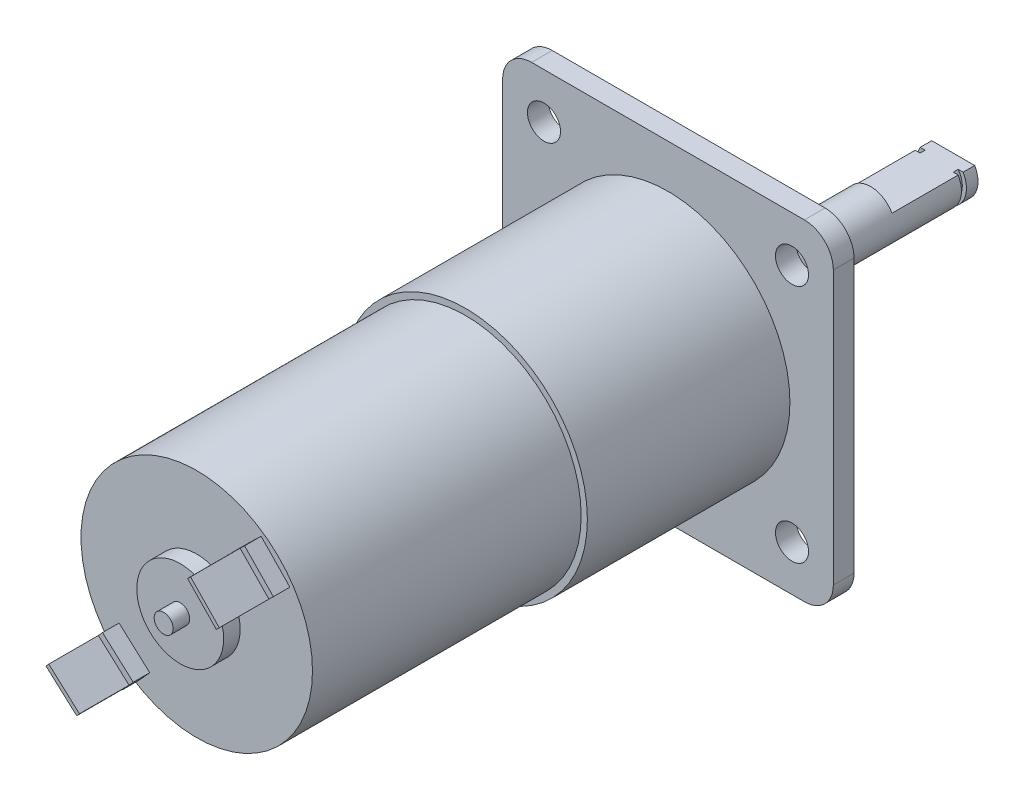
SolidWorks part; units mm, degrees
ref_plane "Alzado" through (0, 0, 0) normal (0, 0, 1) x (1, 0, 0)
ref_plane "Planta" through (0, 0, 0) normal (0, 1, 0) x (1, 0, 0)
ref_plane "Vista lateral" through (0, 0, 0) normal (1, 0, 0) x (0, 0, -1)
sketch "Croquis1" plane through (0, 0, 0) normal (0, 0, 1) x (1, 0, 0)
  circle A0 centre (0, 0) radius 3
  dimension "D1" = 6
extrude "Saliente-Extruir1" add sketch "Croquis1" along normal blind 20
sketch "Croquis3" plane through (0, 0, 20) normal (0, 0, 1) x (1, 0, 0)
  circle A0 centre (0, 0) radius 6.5
  dimension "D1" = 13
extrude "Saliente-Extruir2" add sketch "Croquis3" along normal blind 12
sketch "Croquis4" plane through (0, 0, 32) normal (0, 0, 1) x (1, 0, 0)
  line L0 (17, 14.5) -> (17, 11.7701) construction
  line L1 (16.5, -20) -> (-16.5, -20)
  line L2 (20, -16.5) -> (20, 16.5)
  line L3 (16.5, 20) -> (-16.5, 20)
  line L4 (-20, -16.5) -> (-20, 16.5)
  line L5 (20, -20) -> (-20, 20) construction
  line L6 (20, 20) -> (-20, -20) construction
  line L7 (15, 16.5) -> (11.5735, 16.5) construction
  line L8 (-20, 0) -> (20, 0) construction
  line L9 (0, -20) -> (0, 20) construction
  line L10 (15, 14.5) -> (15, -14.5) construction
  arc A0 (20, 16.5) -> (16.5, 20) centre (16.5, 16.5) ccw
  arc A1 (20, -16.5) -> (16.5, -20) centre (16.5, -16.5) cw
  arc A2 (-16.5, -20) -> (-20, -16.5) centre (-16.5, -16.5) cw
  arc A3 (-20, 16.5) -> (-16.5, 20) centre (-16.5, 16.5) cw
  circle A4 centre (15, 14.5) radius 2
  circle A5 centre (15, -14.5) radius 2
  circle A6 centre (-15, -14.5) radius 2
  circle A7 centre (-15, 14.5) radius 2
  point P0 (0, 0)
  dimension "D3" = 3.5
  dimension "D6" = 4
  dimension "D1" = 40
  dimension "D2" = 40
  dimension "D4" = 3
  dimension "D5" = 3.5
extrude "Saliente-Extruir3" add sketch "Croquis4" along normal blind 2.5
sketch "Croquis5" plane through (0, 0, 34.5) normal (0, 0, 1) x (1, 0, 0)
  circle A0 centre (0, 0) radius 14.75
  dimension "D1" = 29.5
extrude "Saliente-Extruir4" add sketch "Croquis5" along normal blind 24.5
sketch "Croquis6" plane through (0, 0, 59) normal (0, 0, 1) x (1, 0, 0)
  circle A0 centre (0, 0) radius 14
  dimension "D1" = 28
extrude "Saliente-Extruir5" add sketch "Croquis6" along normal blind 32.5
sketch "Croquis7" plane through (0, 0, 91.5) normal (0, 0, 1) x (1, 0, 0)
  circle A0 centre (0, 0) radius 5.25
  dimension "D1" = 10.5
extrude "Saliente-Extruir6" add sketch "Croquis7" along normal blind 2 contours A0
sketch "Croquis8" plane through (0, 0, 93.5) normal (0, 0, 1) x (1, 0, 0)
  circle A0 centre (0, 0) radius 1.15
  dimension "D1" = 2.3
extrude "Saliente-Extruir7" add sketch "Croquis8" along normal blind 2
sketch "Croquis9" plane through (0, 0, 91.5) normal (0, 0, 1) x (1, 0, 0)
  line L0 (15, 14.5) -> (-15, -14.5) construction
  line L1 (8.0886, 7.819) -> (6.3511, 9.6165)
  line L2 (3.7747, 3.6489) -> (-0.9148, 8.5) construction
  line L3 (9.5266, 9.209) -> (7.789, 11.0065)
  line L4 (8.0886, 7.819) -> (9.8262, 6.0215)
  line L5 (9.5266, 9.209) -> (11.2642, 7.4116)
  line L6 (6.3511, 9.6165) -> (7.789, 11.0065)
  line L7 (9.8262, 6.0215) -> (11.2642, 7.4116)
  line L8 (8.0886, 7.819) -> (3.9924, 12.0565) construction
  line L9 (9.5266, 9.209) -> (5.4304, 13.4465) construction
  line L10 (0, 0) -> (-15, 14.5) construction
  line L11 (-9.3957, -6.6733) -> (-10.7362, -8.1576)
  line L12 (-8.8809, -9.8332) -> (-10.7362, -8.1576)
  line L13 (-8.8809, -9.8332) -> (-7.0256, -11.5088)
  line L14 (-5.6851, -10.0246) -> (-7.0256, -11.5088)
  line L15 (-7.5404, -8.3489) -> (-5.6851, -10.0246)
  line L16 (-7.5404, -8.3489) -> (-9.3957, -6.6733)
  circle A0 centre (0, 0) radius 5.25 construction
  dimension "D1" = 6
  dimension "D3" = 2.5
  dimension "D2" = 2
extrude "Saliente-Extruir8" add sketch "Croquis9" along normal blind 2 contours L11 L12 L13 L14 L15 L16 | L6 L3 L5 L7 L4 L1
sketch "Croquis10" plane through (0, 0, 93.5) normal (0, 0, 1) x (1, 0, 0)
  line L0 (-6.3553, -10.7667) -> (-10.066, -7.4154) construction
  line L1 (-5.6851, -10.0246) -> (-7.0256, -11.5088) construction
  line L2 (-9.3957, -6.6733) -> (-10.7362, -8.1576) construction
  line L3 (-6.1878, -10.5812) -> (-9.8984, -7.2299)
  line L4 (-6.5229, -10.9523) -> (-10.2335, -7.601)
  line L5 (-6.5229, -10.9523) -> (-6.1878, -10.5812)
  line L6 (-9.8984, -7.2299) -> (-10.2335, -7.601)
  line L7 (15, -14.5) -> (-15, 14.5) construction
  line L8 (10.5452, 6.7165) -> (7.0701, 10.3115) construction
  line L9 (6.8903, 10.1377) -> (7.2498, 10.4852)
  line L10 (10.7249, 6.8903) -> (10.3654, 6.5428)
  line L11 (10.7249, 6.8903) -> (7.2498, 10.4852)
  line L12 (10.3654, 6.5428) -> (6.8903, 10.1377)
  dimension "D1" = 0.25
  dimension "D2" = 0.25
extrude "Saliente-Extruir9" add sketch "Croquis10" along normal blind 6
sketch "Croquis11" plane through (0, 0, 0) normal (0, 0, -1) x (-1, 0, 0)
  line L0 (-2.5981, 1.5) -> (2.5981, 1.5)
  line L1 (0, -3) -> (3.788, -3) construction
  circle A0 centre (0, 0) radius 3 construction
  circle A1 centre (0, 0) radius 3 construction
  arc A2 (2.5981, 1.5) -> (-2.5981, 1.5) centre (0, 0) ccw
  dimension "D1" = 4.5
  dimension "D2" = 1.5
extrude "Cortar-Extruir1" cut sketch "Croquis11" against normal blind 10
sketch "Croquis12" plane through (0, 0, 0) normal (0, 1, 0) x (1, 0, 0)
  line L0 (-3, -1.4) -> (-2.5, -1.4)
  line L1 (-3, 0) -> (-3, -20) construction
  line L2 (-2.5, -1.4) -> (-2.5, -2)
  line L3 (-2.5, -2) -> (-3, -2)
  line L4 (3, 0) -> (-3, 0) construction
  line L5 (-3, -1.4) -> (-3, -2)
  dimension "D1" = 2
  dimension "D2" = 0.6
  dimension "D3" = 2.5
revolve "Cortar-Revolución1" cut sketch "Croquis12" angle 360 about axis through (0, 0, 20) along (0, 0, -1)
